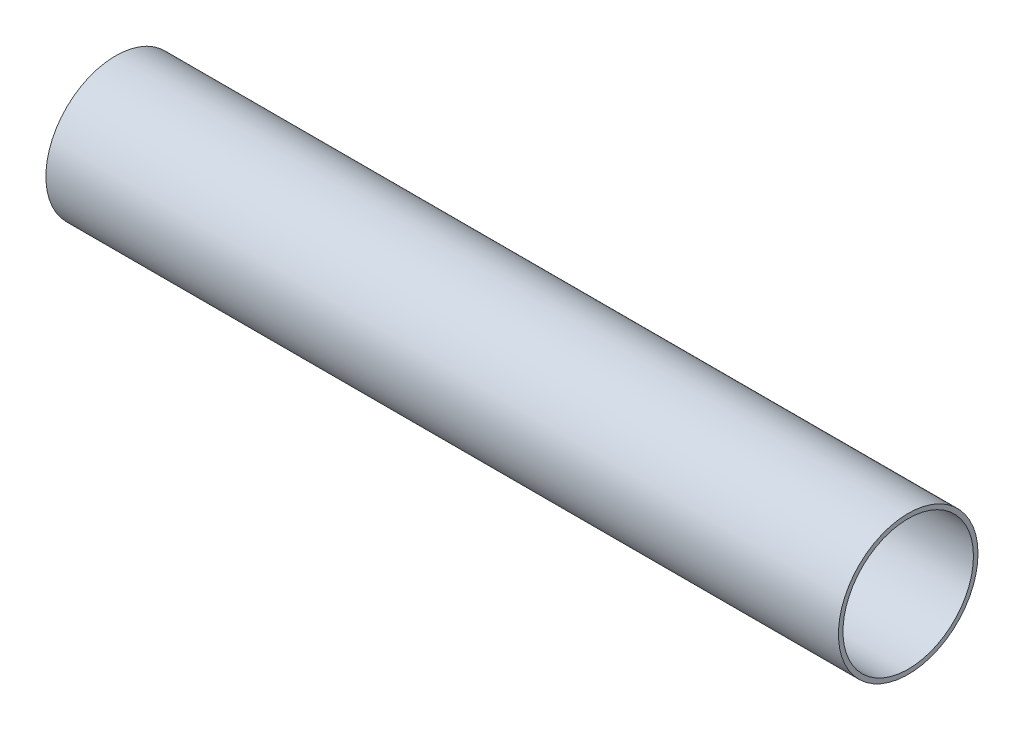
SolidWorks part; units mm, degrees
ref_plane "Front Plane" through (0, 0, 0) normal (0, 0, 1) x (1, 0, 0)
ref_plane "Top Plane" through (0, 0, 0) normal (0, 1, 0) x (1, 0, 0)
ref_plane "Right Plane" through (0, 0, 0) normal (1, 0, 0) x (0, 0, -1)
sketch "Sketch1" plane through (0, 0, 0) normal (1, 0, 0) x (0, 0, -1)
  circle A0 centre (0, 0) radius 45.847
  circle A1 centre (0, 0) radius 42.8625
  dimension "D1" = 91.694
  dimension "D2" = 85.725
extrude "Boss-Extrude1" add sketch "Sketch1" along normal blind 520.7
